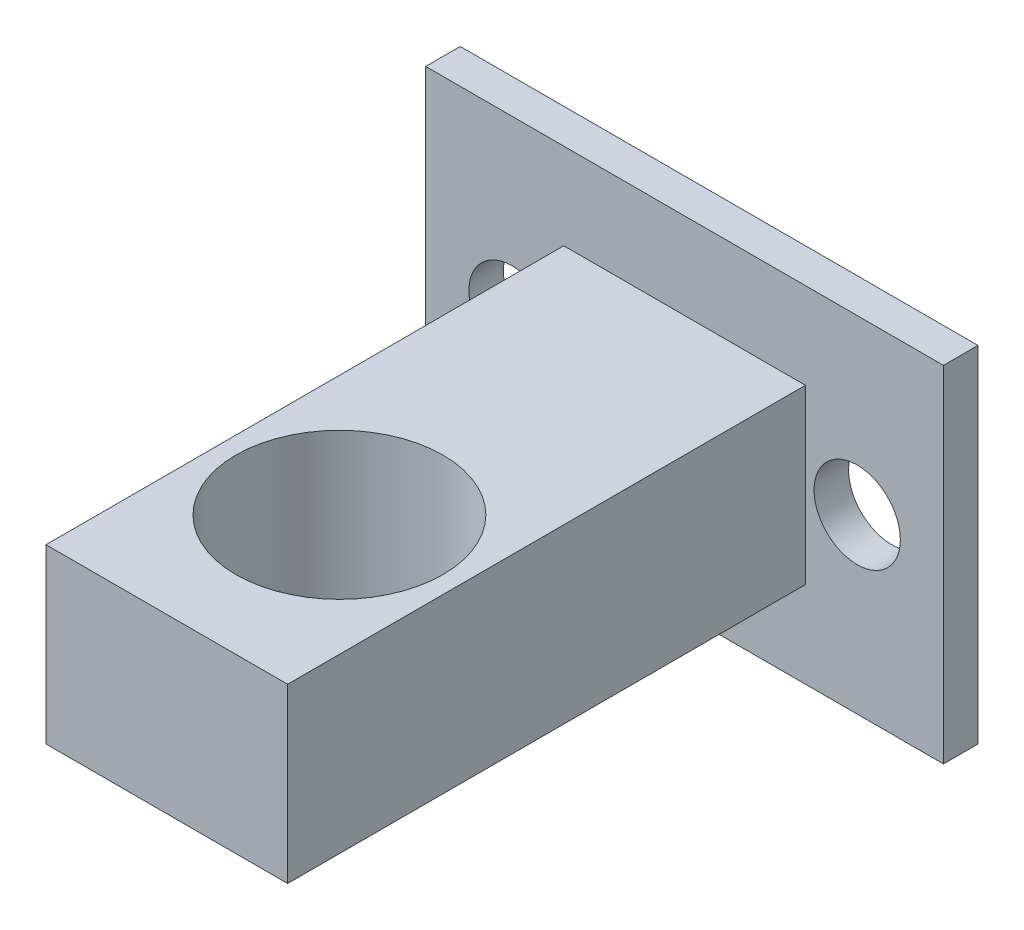
SolidWorks part; units mm, degrees
ref_plane "前视基准面" through (0, 0, 0) normal (0, 0, 1) x (1, 0, 0)
ref_plane "上视基准面" through (0, 0, 0) normal (0, 1, 0) x (1, 0, 0)
ref_plane "右视基准面" through (0, 0, 0) normal (1, 0, 0) x (0, 0, -1)
sketch "草图1" plane through (0, 0, 0) normal (0, 0, 1) x (1, 0, 0)
  line L0 (-30.8219, 18.4932) -> (-0.8219, 18.4932)
  line L1 (-0.8219, 18.4932) -> (-0.8219, 8.4932)
  line L2 (-0.8219, 8.4932) -> (-0.8219, -1.5068)
  line L3 (-0.8219, -1.5068) -> (-30.8219, -1.5068)
  line L4 (-30.8219, -1.5068) -> (-30.8219, 18.4932)
  line L5 (-30.8219, 8.4932) -> (-25.8219, 8.4932) construction
  line L6 (-25.8219, 8.4932) -> (-5.8219, 8.4932) construction
  circle A0 centre (-25.8219, 8.4932) radius 2.5
  circle A1 centre (-5.8219, 8.4932) radius 2.5
  dimension "D6" = 5
  dimension "D3" = 5
  dimension "D1" = 30
  dimension "D2" = 20
  dimension "D4" = 5
extrude "凸台-拉伸1" add sketch "草图1" along normal blind 2
sketch "草图2" plane through (0, 0, 2) normal (0, 0, 1) x (1, 0, 0)
  line L0 (-30.8219, 8.4932) -> (-0.8219, 8.4932) construction
  line L1 (-30.8219, 18.4932) -> (-30.8219, -1.5068) construction
  line L2 (-0.8219, -1.5068) -> (-0.8219, 18.4932) construction
  line L3 (-15.8219, -1.5068) -> (-15.8219, 18.4932) construction
  line L4 (-30.8219, -1.5068) -> (-0.8219, -1.5068) construction
  line L5 (-0.8219, 18.4932) -> (-30.8219, 18.4932) construction
  line L6 (-22.8219, 3.4932) -> (-8.8219, 3.4932)
  line L7 (-15.8219, 13.4932) -> (-22.8219, 13.4932)
  line L8 (-22.8219, 13.4932) -> (-22.8219, 3.4932)
  line L9 (-8.8219, 3.4932) -> (-8.8219, 13.4932)
  line L10 (-8.8219, 13.4932) -> (-15.8219, 13.4932)
  dimension "D1" = 5
  dimension "D2" = 7
  dimension "D3" = 10
  dimension "D4" = 14
extrude "凸台-拉伸2" add sketch "草图2" along normal blind 30
sketch "草图4" plane through (0, 3.4932, 0) normal (0, -1, 0) x (1, 0, 0)
  line L0 (-15.8219, 2) -> (-15.8219, 22) construction
  line L1 (-22.8219, 2) -> (-8.8219, 2) construction
  circle A0 centre (-15.8219, 22) radius 6
  dimension "D2" = 12
  dimension "D1" = 20
extrude "切除-拉伸1" cut sketch "草图4" against normal blind 15
